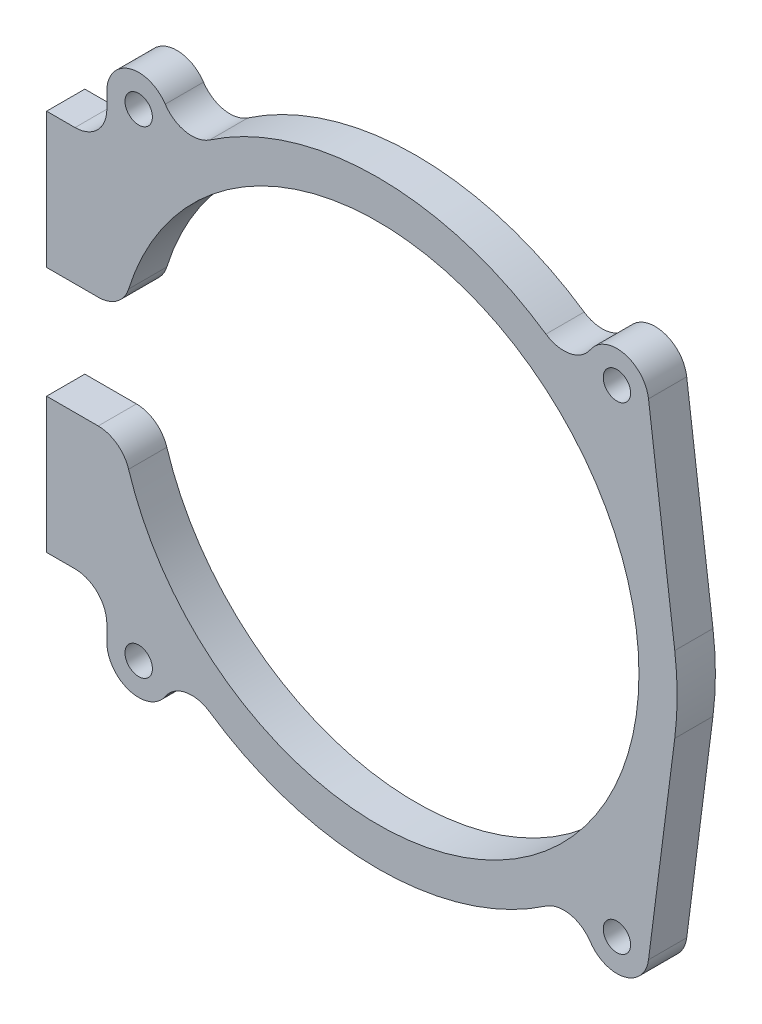
SolidWorks part; units mm, degrees
ref_plane "前视基准面" through (0, 0, 0) normal (0, 0, 1) x (1, 0, 0)
ref_plane "上视基准面" through (0, 0, 0) normal (0, 1, 0) x (1, 0, 0)
ref_plane "右视基准面" through (0, 0, 0) normal (1, 0, 0) x (0, 0, -1)
sketch "草图1" plane through (0, 0, 0) normal (0, 0, 1) x (1, 0, 0)
  line L0 (0, 0) -> (50000, 0) construction
  line L1 (-52, 8.75) -> (-52, -8.75) construction
  line L2 (-52, 8.75) -> (-52, 30)
  line L3 (-52, -8.75) -> (-52, -30)
  line L4 (-52, 8.75) -> (-43.8969, 8.75)
  line L5 (-52, -8.75) -> (-43.8969, -8.75)
  line L6 (-42.54, 37.5) -> (-42.54, 35)
  line L7 (-47.54, 30) -> (-52, 30)
  line L8 (-47.54, -30) -> (-52, -30)
  line L9 (-42.54, -37.5) -> (-42.54, -35)
  line L10 (0, 0) -> (0, -50000) construction
  line L11 (42.4995, 38.1352) -> (46.6192, 5.9711)
  line L12 (42.4995, -38.1352) -> (46.6192, -5.9711)
  arc A0 (-39.1255, -12.2554) -> (-39.1255, 12.2554) centre (0, 0) ccw
  arc A1 (-40.0554, 8.75) -> (-40.0554, -8.75) centre (0, 0) ccw construction
  circle A2 centre (-37.54, 37.5) radius 2.15
  circle A3 centre (-37.54, -37.5) radius 2.15
  arc A4 (-33.3722, 40.2622) -> (-42.54, 37.5) centre (-37.54, 37.5) ccw
  arc A5 (-42.54, -37.5) -> (-33.3722, -40.2622) centre (-37.54, -37.5) ccw
  arc A6 (-26.3963, -38.8874) -> (26.3963, -38.8874) centre (0, 0) ccw
  arc A7 (-33.3722, 40.2622) -> (-26.3963, 38.8874) centre (-29.2045, 43.0244) ccw
  arc A8 (-33.3722, -40.2622) -> (-42.54, -37.5) centre (-37.54, -37.5) cw
  arc A9 (-33.3722, -40.2622) -> (-26.3963, -38.8874) centre (-29.2045, -43.0244) cw
  circle A10 centre (37.54, -37.5) radius 2.15
  circle A11 centre (37.54, 37.5) radius 2.15
  arc A12 (42.4995, 38.1352) -> (33.3722, 40.2622) centre (37.54, 37.5) ccw
  arc A13 (33.3722, -40.2622) -> (42.4995, -38.1352) centre (37.54, -37.5) ccw
  arc A14 (33.3722, 40.2622) -> (26.3963, 38.8874) centre (29.2045, 43.0244) cw
  arc A15 (33.3722, -40.2622) -> (26.3963, -38.8874) centre (29.2045, -43.0244) ccw
  arc A16 (26.3963, 38.8874) -> (-26.3963, 38.8874) centre (0, 0) ccw
  arc A17 (46.6192, -5.9711) -> (46.6192, 5.9711) centre (0, 0) ccw
  arc A18 (-47.54, -30) -> (-42.54, -35) centre (-47.54, -35) cw
  arc A19 (-42.54, 35) -> (-47.54, 30) centre (-47.54, 35) cw
  arc A20 (-43.8969, 8.75) -> (-39.1255, 12.2554) centre (-43.8969, 13.75) ccw
  arc A21 (-43.8969, -8.75) -> (-39.1255, -12.2554) centre (-43.8969, -13.75) cw
  point P8 (-52, 0)
  point P44 (-42.54, -30)
  point P47 (-42.54, 30)
  dimension "D1" = 82
  dimension "D5" = 4.3
  dimension "D6" = 75
  dimension "D8" = 10
  dimension "D9" = 94
  dimension "D10" = 5
  dimension "D11" = 10
  dimension "D12" = 5
  dimension "D13" = 5
  dimension "D14" = 5
  dimension "D15" = 5
  dimension "D2" = 17.5
  dimension "D3" = 52
  dimension "D4" = 60
  dimension "D7" = 14.46
extrude "凸台-拉伸1" add sketch "草图1" along normal blind 6 contours A21 L5 L3 L8 A18 L9 A5 A9 A6 A15 A13 L12 A17 L11 A12 A14 A16 A7 A4 L6 A19 L7 L2 L4 A20 A0 A10 A3 A2 A11
